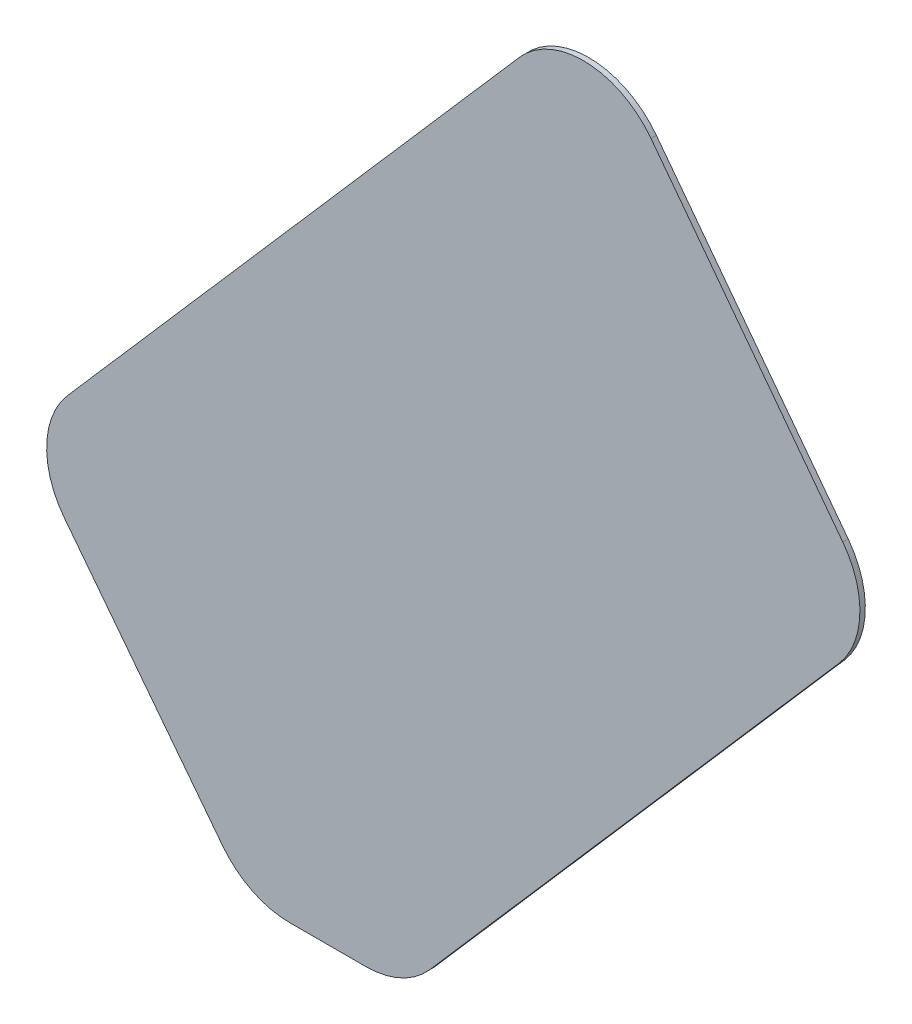
SolidWorks part; units mm, degrees
ref_plane "Front Plane" through (0, 0, 0) normal (0, 0, 1) x (1, 0, 0)
ref_plane "Top Plane" through (0, 0, 0) normal (0, 1, 0) x (1, 0, 0)
ref_plane "Right Plane" through (0, 0, 0) normal (1, 0, 0) x (0, 0, -1)
sketch "Sketch1" plane through (0, 0, 0) normal (0, 0, 1) x (1, 0, 0)
  line L1 (-213.4997, 186.4975) -> (53.0188, 492.5426)
  line L5 (1.4475, 220.1452) -> (5.3878, 224.6699) construction
  line L6 (-215.353, 123.0826) -> (-121.9592, 2.258)
  line L7 (-82.3996, -17.1636) -> (-37.7063, -17.1636)
  line L8 (0, 0) -> (241.5236, 277.3433)
  line L10 (71.3996, 158.1236) -> (75.34, 162.6484) construction
  line L11 (243.6956, 340.3412) -> (130.6035, 489.8676)
  line L12 (-199.3163, 102.3358) -> (-378.1569, 333.7039)
  line L17 (-60, 32.8364) -> (-50, 32.8364)
  line L18 (-60, 32.8364) -> (-60, 22.8364)
  line L19 (-60, 22.8364) -> (-50, 22.8364)
  line L20 (-50, 32.8364) -> (-50, 22.8364)
  line L21 (158.3399, 453.1955) -> (-26.8585, 698.0583)
  circle A0 centre (192.4604, 368.7724) radius 11.15
  circle A5 centre (-135.6677, 56.5626) radius 11.15
  arc A6 (241.5236, 277.3433) -> (243.6956, 340.3412) centre (203.8172, 310.1798) ccw
  arc A7 (-121.9592, 2.258) -> (-82.3996, -17.1636) centre (-82.3996, 32.8364) ccw
  arc A8 (-37.7063, -17.1636) -> (0, 0) centre (-37.7063, 32.8364) ccw
  arc A9 (-215.353, 123.0826) -> (-213.4997, 186.4975) centre (-175.7934, 153.661) cw
  arc A10 (53.0188, 492.5426) -> (130.6035, 489.8676) centre (90.7251, 459.7062) cw
  point P7 (-55, 22.8364)
  point P9 (3.4177, 222.4075)
  point P23 (-106.9468, -17.1636)
  point P26 (-14.9468, -17.1636)
  dimension "D3" = 22.3
  dimension "D6" = 22.3
  dimension "D12" = 50
  dimension "D18" = 405.8272
  dimension "D1" = 140
  dimension "D2" = 50
  dimension "D4" = 23.713
  dimension "D5" = 97.044
  dimension "D7" = 22.3648
  dimension "D8" = 139.4569
  dimension "D9" = 92
  dimension "D10" = 127.703
  dimension "D11" = 78.152
  dimension "D13" = 10
  dimension "D14" = 10
  dimension "D15" = 40
  dimension "D16" = 367.7675
  dimension "D17" = 152.7121
  dimension "D19" = 50
  dimension "D22" = 139.4569
extrude "Boss-Extrude1" add sketch "Sketch1" along normal mid plane 3.175 contours L6 A7 L7 A8 L8 A6 L11 A10 L1 A9
scale "Scale1" scale about origin uniform scaling yes scale factor 0.8
